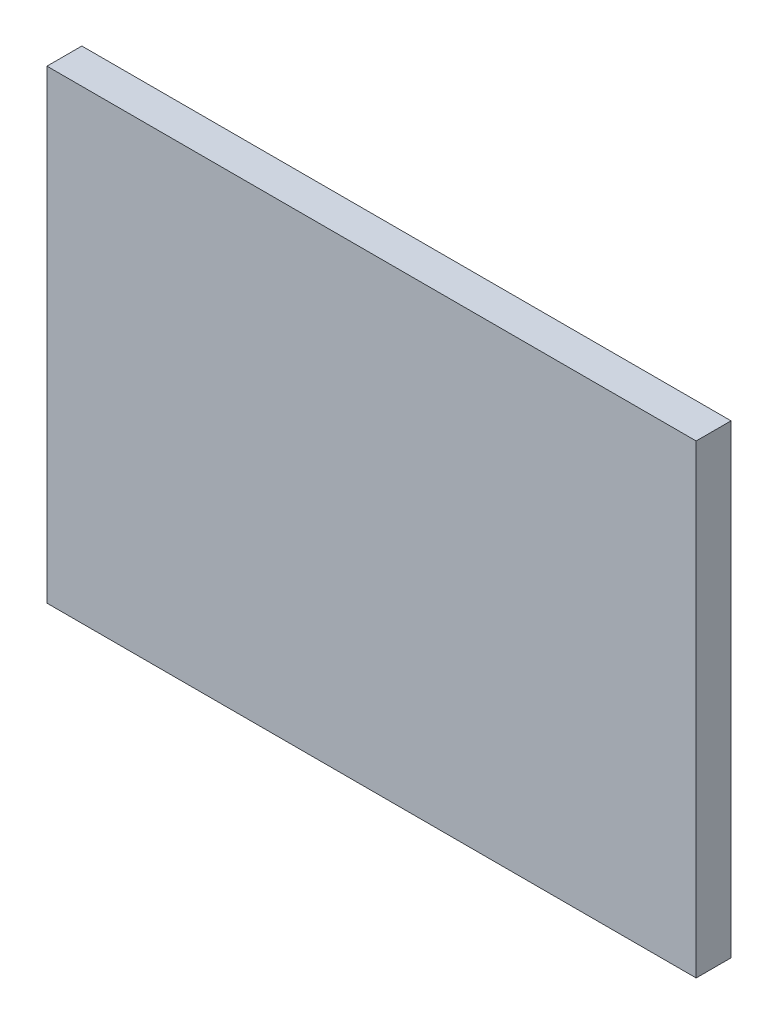
SolidWorks part; units mm, degrees
material "Pine"
ref_plane "Front Plane" through (0, 0, 0) normal (0, 0, 1) x (1, 0, 0)
ref_plane "Top Plane" through (0, 0, 0) normal (0, 1, 0) x (1, 0, 0)
ref_plane "Right Plane" through (0, 0, 0) normal (1, 0, 0) x (0, 0, -1)
sketch "Sketch1" plane through (0, 0, 0) normal (0, 0, 1) x (1, 0, 0)
  line L0 (-5300.6625, 1520.825) -> (-5451.475, 1520.825)
  line L1 (-5456.2375, 1384.3) -> (-5456.2375, 1516.0625)
  line L2 (-5557.8375, 1546.225) -> (-5194.3, 1546.225)
  line L3 (-5557.8375, 1539.875) -> (-5194.3, 1539.875)
  line L4 (-5297.4875, 1377.95) -> (-5454.65, 1377.95)
  line L5 (-5291.1375, 1384.3) -> (-5291.1375, 1516.0625)
  line L6 (-5300.6625, 1525.5875) -> (-5451.475, 1525.5875)
  line L7 (-5461, 1384.3) -> (-5461, 1516.0625)
  line L8 (-5297.4875, 1382.7125) -> (-5454.65, 1382.7125)
  line L9 (-5295.9, 1384.3) -> (-5295.9, 1516.0625)
  line L10 (-5740.4, 998.5375) -> (-5740.4, 1181.1)
  line L11 (-5740.4, 1181.1) -> (-5512.5938, 1181.1)
  line L12 (-5512.5938, 1181.1) -> (-5512.5938, 998.5375)
  line L13 (-5512.5938, 998.5375) -> (-5740.4, 998.5375)
  line L14 (-5258.5938, 1181.1) -> (-5486.4, 1181.1)
  line L15 (-5258.5938, 998.5375) -> (-5258.5938, 1181.1)
  line L16 (-5486.4, 998.5375) -> (-5258.5938, 998.5375)
  line L17 (-5486.4, 1181.1) -> (-5486.4, 998.5375)
  line L18 (-5740.4, 898.525) -> (-5011.7375, 898.525)
  line L19 (-5168.1062, 1384.3) -> (-5168.1062, 1392.2375)
  line L20 (-5176.0437, 1400.175) -> (-5245.8937, 1400.175)
  line L21 (-5253.8313, 1392.2375) -> (-5253.8313, 1384.3)
  line L22 (-5451.475, 1512.8875) -> (-5451.475, 1384.3)
  line L23 (-5303.8375, 1516.0625) -> (-5448.3, 1516.0625)
  line L24 (-5498.3062, 1384.3) -> (-5451.475, 1384.3)
  line L25 (-5253.8313, 1384.3) -> (-5300.6625, 1384.3)
  line L26 (-5584.0312, 1384.3) -> (-5740.4, 1384.3)
  line L27 (-5564.1875, 1536.7) -> (-5740.4, 1536.7)
  line L28 (-5740.4, 1357.3125) -> (-5740.4, 1206.5)
  line L29 (-5011.7375, 1357.3125) -> (-5740.4, 1357.3125)
  line L30 (-5011.7375, 1206.5) -> (-5011.7375, 1357.3125)
  line L31 (-5740.4, 1206.5) -> (-5011.7375, 1206.5)
  line L32 (-4765.675, 1549.4) -> (-4978.4, 1549.4)
  line L33 (-4765.675, 1397) -> (-4765.675, 1549.4)
  line L34 (-4978.4, 1397) -> (-4765.675, 1397)
  line L35 (-4978.4, 1549.4) -> (-4978.4, 1397)
  line L36 (-4765.675, 1371.6) -> (-4978.4, 1371.6)
  line L37 (-4765.675, 1219.2) -> (-4765.675, 1371.6)
  line L38 (-4978.4, 1219.2) -> (-4765.675, 1219.2)
  line L39 (-4978.4, 1371.6) -> (-4978.4, 1219.2)
  line L40 (-5284.7875, 803.275) -> (-5272.0875, 803.275)
  line L41 (-5187.95, 1536.7) -> (-5011.7375, 1536.7)
  line L42 (-5300.6625, 1384.3) -> (-5300.6625, 1512.8875)
  line L43 (-5740.4, 1536.7) -> (-5740.4, 1384.3)
  line L44 (-5557.8375, 1536.7) -> (-5557.8375, 1549.4)
  line L45 (-5557.8375, 1549.4) -> (-5194.3, 1549.4)
  line L46 (-5194.3, 1549.4) -> (-5194.3, 1536.7)
  line L47 (-5011.7375, 1536.7) -> (-5011.7375, 1384.3)
  line L48 (-5011.7375, 1384.3) -> (-5168.1062, 1384.3)
  line L49 (-5498.3062, 1384.3) -> (-5498.3062, 1392.2375)
  line L50 (-5506.2437, 1400.175) -> (-5576.0938, 1400.175)
  line L51 (-5584.0312, 1392.2375) -> (-5584.0312, 1384.3)
  line L52 (-5740.4, 660.4) -> (-5740.4, 898.525)
  line L53 (-5011.7375, 898.525) -> (-5011.7375, 660.4)
  line L54 (-5011.7375, 660.4) -> (-5740.4, 660.4)
  line L55 (-5291.1375, 803.275) -> (-5291.1375, 752.475)
  line L56 (-5265.7375, 752.475) -> (-5265.7375, 803.275)
  line L57 (-5284.7875, 752.475) -> (-5272.0875, 752.475)
  arc A0 (-5451.475, 1520.825) -> (-5456.2375, 1516.0625) centre (-5451.475, 1516.0625) ccw
  arc A1 (-5461, 1384.3) -> (-5454.65, 1377.95) centre (-5454.65, 1384.3) ccw
  arc A2 (-5297.4875, 1377.95) -> (-5291.1375, 1384.3) centre (-5297.4875, 1384.3) ccw
  circle A3 centre (-5037.9312, 1233.4875) radius 1.5875
  circle A4 centre (-5037.9312, 1328.7375) radius 1.5875
  circle A5 centre (-5714.2063, 1233.4875) radius 1.5875
  circle A6 centre (-5714.2063, 1328.7375) radius 1.5875
  circle A7 centre (-5018.0875, 1333.5) radius 1.5875
  circle A8 centre (-5018.0875, 1231.9) radius 1.5875
  circle A9 centre (-5734.05, 1231.9) radius 1.5875
  circle A10 centre (-5734.05, 1333.5) radius 1.5875
  circle A11 centre (-5734.05, 1511.3) radius 1.5875
  circle A12 centre (-5734.05, 1409.7) radius 1.5875
  circle A13 centre (-5018.0875, 1511.3) radius 1.5875
  circle A14 centre (-5018.0875, 1409.7) radius 1.5875
  arc A15 (-5557.8375, 1546.225) -> (-5557.8375, 1539.875) centre (-5557.8375, 1543.05) ccw
  arc A16 (-5194.3, 1539.875) -> (-5194.3, 1546.225) centre (-5194.3, 1543.05) ccw
  arc A17 (-5291.1375, 1516.0625) -> (-5300.6625, 1525.5875) centre (-5300.6625, 1516.0625) ccw
  arc A18 (-5451.475, 1525.5875) -> (-5461, 1516.0625) centre (-5451.475, 1516.0625) ccw
  arc A19 (-5456.2375, 1384.3) -> (-5454.65, 1382.7125) centre (-5454.65, 1384.3) ccw
  arc A20 (-5297.4875, 1382.7125) -> (-5295.9, 1384.3) centre (-5297.4875, 1384.3) ccw
  arc A21 (-5295.9, 1516.0625) -> (-5300.6625, 1520.825) centre (-5300.6625, 1516.0625) ccw
  circle A22 centre (-5702.3, 892.175) radius 1.5875
  circle A23 centre (-5734.05, 860.425) radius 1.5875
  circle A24 centre (-5474.8906, 892.175) radius 1.5875
  circle A25 centre (-5277.2469, 892.175) radius 1.5875
  circle A26 centre (-5049.8375, 892.175) radius 1.5875
  circle A27 centre (-5018.0875, 860.425) radius 1.5875
  circle A28 centre (-5296.6938, 1174.75) radius 1.5875
  circle A29 centre (-5448.3, 1174.75) radius 1.5875
  circle A30 centre (-5264.9437, 1155.7) radius 1.5875
  circle A31 centre (-5264.9437, 1023.9375) radius 1.5875
  circle A32 centre (-5518.9438, 1155.7) radius 1.5875
  circle A33 centre (-5518.9438, 1023.9375) radius 1.5875
  circle A34 centre (-5702.3, 1004.8875) radius 1.5875
  circle A35 centre (-5550.6937, 1004.8875) radius 1.5875
  arc A36 (-5576.0938, 1400.175) -> (-5584.0312, 1392.2375) centre (-5576.0938, 1392.2375) ccw
  arc A37 (-5168.1062, 1392.2375) -> (-5176.0437, 1400.175) centre (-5176.0437, 1392.2375) ccw
  arc A38 (-5245.8937, 1400.175) -> (-5253.8313, 1392.2375) centre (-5245.8937, 1392.2375) ccw
  arc A39 (-5448.3, 1516.0625) -> (-5451.475, 1512.8875) centre (-5448.3, 1512.8875) ccw
  arc A40 (-5284.7875, 803.275) -> (-5291.1375, 803.275) centre (-5287.9625, 803.275) ccw
  circle A41 centre (-5679.2812, 1026.3187) radius 1.5875
  circle A42 centre (-5679.2812, 1153.3187) radius 1.5875
  circle A43 centre (-5571.3313, 1153.3187) radius 1.5875
  circle A44 centre (-5571.3313, 1026.3187) radius 1.5875
  circle A45 centre (-5317.3312, 1153.3187) radius 1.5875
  circle A46 centre (-5317.3312, 1026.3187) radius 1.5875
  circle A47 centre (-5425.2812, 1026.3187) radius 1.5875
  circle A48 centre (-5425.2812, 1153.3187) radius 1.5875
  arc A49 (-5194.3, 1536.7) -> (-5187.95, 1536.7) centre (-5191.125, 1536.7) ccw
  arc A50 (-5564.1875, 1536.7) -> (-5557.8375, 1536.7) centre (-5561.0125, 1536.7) ccw
  arc A51 (-5300.6625, 1512.8875) -> (-5303.8375, 1516.0625) centre (-5303.8375, 1512.8875) ccw
  arc A52 (-5498.3062, 1392.2375) -> (-5506.2437, 1400.175) centre (-5506.2437, 1392.2375) ccw
  circle A53 centre (-5712.46, 784.225) radius 4.7625
  arc A54 (-5272.0875, 752.475) -> (-5265.7375, 752.475) centre (-5268.9125, 752.475) ccw
  arc A55 (-5291.1375, 752.475) -> (-5284.7875, 752.475) centre (-5287.9625, 752.475) ccw
  circle A56 centre (-5182.3938, 684.2125) radius 3.175
  circle A57 centre (-5239.5437, 684.2125) radius 3.175
  circle A58 centre (-5512.5938, 684.2125) radius 3.175
  circle A59 centre (-5569.7437, 684.2125) radius 3.175
  circle A60 centre (-5474.8906, 666.75) radius 1.5875
  circle A61 centre (-5277.2469, 666.75) radius 1.5875
  circle A62 centre (-5734.05, 698.5) radius 1.5875
  circle A63 centre (-5702.3, 666.75) radius 1.5875
  circle A64 centre (-5049.8375, 666.75) radius 1.5875
  circle A65 centre (-5018.0875, 698.5) radius 1.5875
  circle A66 centre (-5713.73, 835.025) radius 4.7625
  circle A67 centre (-5712.46, 819.785) radius 4.7625
  circle A68 centre (-5712.46, 802.005) radius 4.7625
  circle A69 centre (-5714.2063, 1314.45) radius 3.175
  circle A70 centre (-5037.9312, 1314.45) radius 3.175
  arc A71 (-5265.7375, 803.275) -> (-5272.0875, 803.275) centre (-5268.9125, 803.275) ccw
  ellipse E0 centre (-5371.3062, 1089.8188) end of major axis (-5277.6438, 1089.8188) minor radius 65.0875
  ellipse E1 centre (-5625.3062, 1089.8188) end of major axis (-5531.6438, 1089.8188) minor radius 65.0875
sketch "SideOutline" plane through (0, 0, 0) normal (0, 0, 1) x (1, 0, 0)
  line L0 (-4765.675, 1371.6) -> (-4765.675, 1219.2)
  line L1 (-4765.675, 1219.2) -> (-4978.4, 1219.2)
  line L2 (-4978.4, 1219.2) -> (-4978.4, 1371.6)
  line L3 (-4978.4, 1371.6) -> (-4765.675, 1371.6)
  line L4 (-4872.0375, 1371.6) -> (-4872.0375, 1219.2) construction
  line L5 (-4872.0375, 1295.4) -> (-4978.4, 1295.4) construction
  line L6 (-4872.0375, 1295.4) -> (-4765.675, 1295.4) construction
  dimension "D1" = 152.4
  dimension "D2" = 212.725
extrude "SideOutline_Thickness" add sketch "SideOutline" against normal blind 11.43
